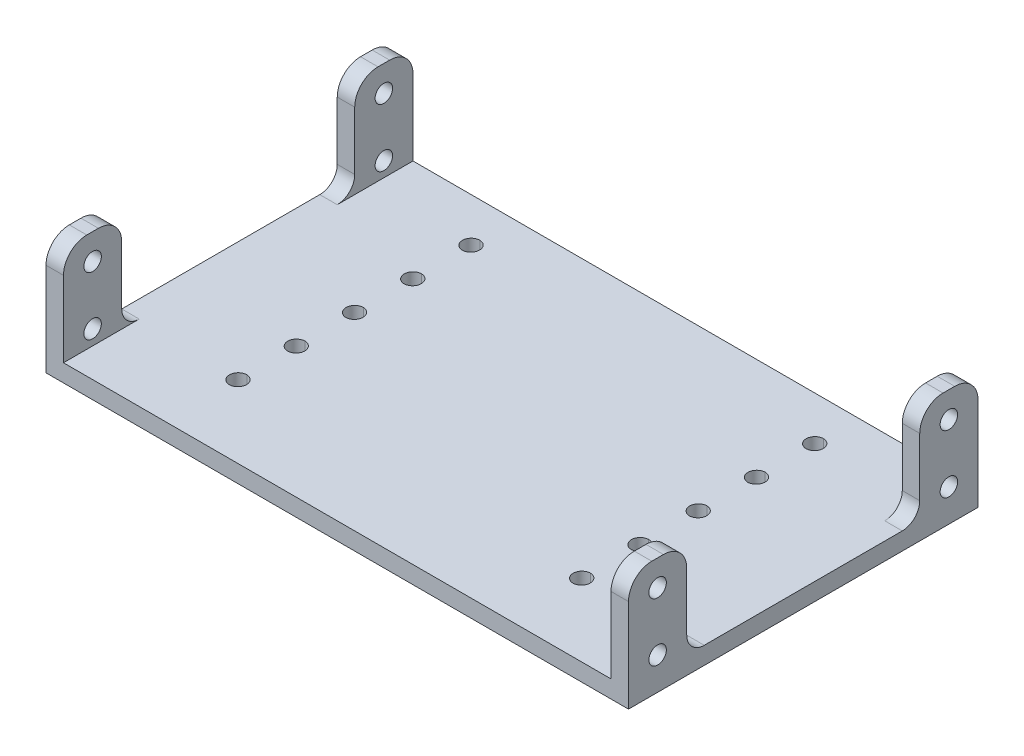
SolidWorks part; units mm, degrees
ref_plane "Front Plane" through (0, 0, 0) normal (0, 0, 1) x (1, 0, 0)
ref_plane "Top Plane" through (0, 0, 0) normal (0, 1, 0) x (1, 0, 0)
ref_plane "Right Plane" through (0, 0, 0) normal (1, 0, 0) x (0, 0, -1)
sketch "Sketch1" plane through (0, 0, 0) normal (0, 1, 0) x (1, 0, 0)
  line L0 (-29.4624, -27.534) -> (-29.4624, -17.534)
  line L1 (-50, -30) -> (50, -30)
  line L2 (-50, -30) -> (-50, 30)
  line L3 (-50, 30) -> (50, 30)
  line L4 (50, -30) -> (50, 30)
  line L5 (-50, -30) -> (50, 30) construction
  line L6 (-50, 30) -> (50, -30) construction
  line L7 (-19.4624, -27.534) -> (19.5376, -27.534)
  line L8 (0.0376, -27.534) -> (0.0376, 27.7543) construction
  circle A0 centre (-29.4624, -17.534) radius 1.5
  circle A1 centre (-29.4624, -7.534) radius 1.5
  circle A2 centre (-29.4624, 2.466) radius 1.5
  circle A3 centre (-29.4624, 12.466) radius 1.5
  circle A4 centre (-29.4624, 22.466) radius 1.5
  circle A5 centre (29.5376, 22.466) radius 1.5
  circle A6 centre (29.5376, 12.466) radius 1.5
  circle A7 centre (29.5376, 2.466) radius 1.5
  circle A8 centre (29.5376, -7.534) radius 1.5
  circle A9 centre (29.5376, -17.534) radius 1.5
  point P0 (0, 0)
  dimension "D4" = 3
  dimension "D1" = 60
  dimension "D2" = 100
  dimension "D3" = 10
extrude "Boss-Extrude1" add sketch "Sketch1" along normal blind 3
sketch "Sketch3" plane through (50, 0, 0) normal (1, 0, 0) x (0, 0, -1)
  line L0 (-25, 3) -> (-25, 5.56)
  line L1 (-30, 3) -> (30, 3)
  line L2 (-30, 3) -> (-30, 20)
  line L3 (-30, 20) -> (30, 20)
  line L4 (30, 3) -> (30, 20)
  line L5 (0, 3) -> (0, 20) construction
  line L7 (-20, 20) -> (20, 20)
  line L8 (-20, 20) -> (-20, 3)
  line L9 (-20, 3) -> (20, 3)
  line L10 (20, 20) -> (20, 3)
  circle A0 centre (-25, 5.56) radius 1.5
  circle A1 centre (-25, 15.56) radius 1.5
  circle A2 centre (25, 5.56) radius 1.5
  circle A3 centre (25, 15.56) radius 1.5
  dimension "D5" = 3
  dimension "D1" = 20
  dimension "D2" = 60
  dimension "D3" = 2.56
  dimension "D4" = 5
  dimension "D7" = 10
  dimension "D8" = 10
  dimension "D6" = 2
extrude "Boss-Extrude2" add sketch "Sketch3" against normal blind 3
sketch "Sketch4" plane through (0, 3, 0) normal (0, 1, 0) x (1, 0, 0)
  line L0 (-50, 30) -> (50, 30)
  line L1 (-50, 30) -> (0, 30)
  line L3 (0, 30) -> (0, -30)
  dimension "D1" = 50
ref_plane "Plane1" through (0, 0, 0) normal (1, 0, 0) x (0, 0, -1)
mirror "Mirror1" about plane through (0, 0, 0) normal (1, 0, 0) of "Boss-Extrude1", "Boss-Extrude2"
fillet "Fillet1" radius 3 4 edges at (48.5, 3, -20) (-48.5, 3, 20) (-48.5, 3, -20)
fillet "Fillet2" radius 4 8 edges at (-48.5, 20, 30) (-48.5, 20, 20) (-48.5, 20, -20) (-48.5, 20, -30) (48.5, 20, -20) (48.5, 20, -30) (48.5, 20, 30) (48.5, 20, 20)
